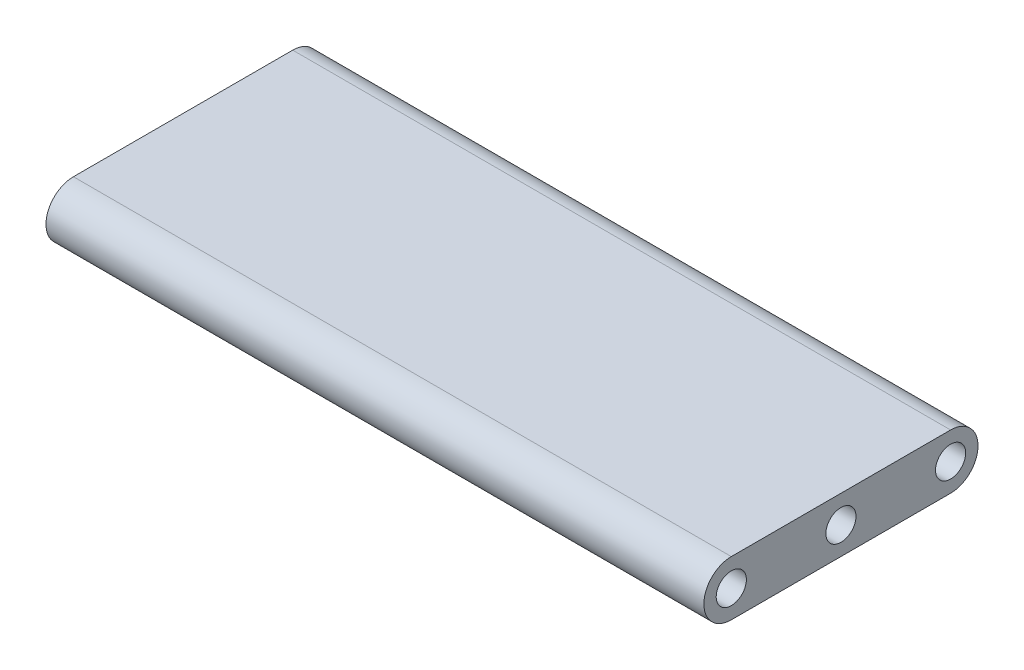
SolidWorks part; units mm, degrees
ref_plane "Front Plane" through (0, 0, 0) normal (0, 0, 1) x (1, 0, 0)
ref_plane "Top Plane" through (0, 0, 0) normal (0, 1, 0) x (1, 0, 0)
ref_plane "Right Plane" through (0, 0, 0) normal (1, 0, 0) x (0, 0, -1)
sketch "Sketch1" plane through (0, 0, 0) normal (1, 0, 0) x (0, 0, -1)
  line L1 (-25.4, -6.35) -> (25.4, -6.35)
  line L2 (-25.4, -6.35) -> (-25.4, 6.35) construction
  line L3 (-25.4, 6.35) -> (25.4, 6.35)
  line L4 (25.4, -6.35) -> (25.4, 6.35) construction
  line L5 (-25.4, -6.35) -> (25.4, 6.35) construction
  line L6 (-25.4, 6.35) -> (25.4, -6.35) construction
  circle A0 centre (-25.4, 0) radius 3.4925
  arc A1 (-25.4, 6.35) -> (-25.4, -6.35) centre (-25.4, 0) ccw
  circle A2 centre (25.4, 0) radius 3.4925
  arc A3 (25.4, -6.35) -> (25.4, 6.35) centre (25.4, 0) ccw
  circle A4 centre (0, 0) radius 3.4925
  point P0 (0, 0)
  dimension "D3" = 6.985
  dimension "D4" = 12.7
  dimension "D1" = 12.7
  dimension "D2" = 50.8
extrude "Boss-Extrude1" add sketch "Sketch1" along normal mid plane 152.4 contours L3 A1 L1 A0 | A2 L3 A0 L1 | L1 A3 L3 A2
